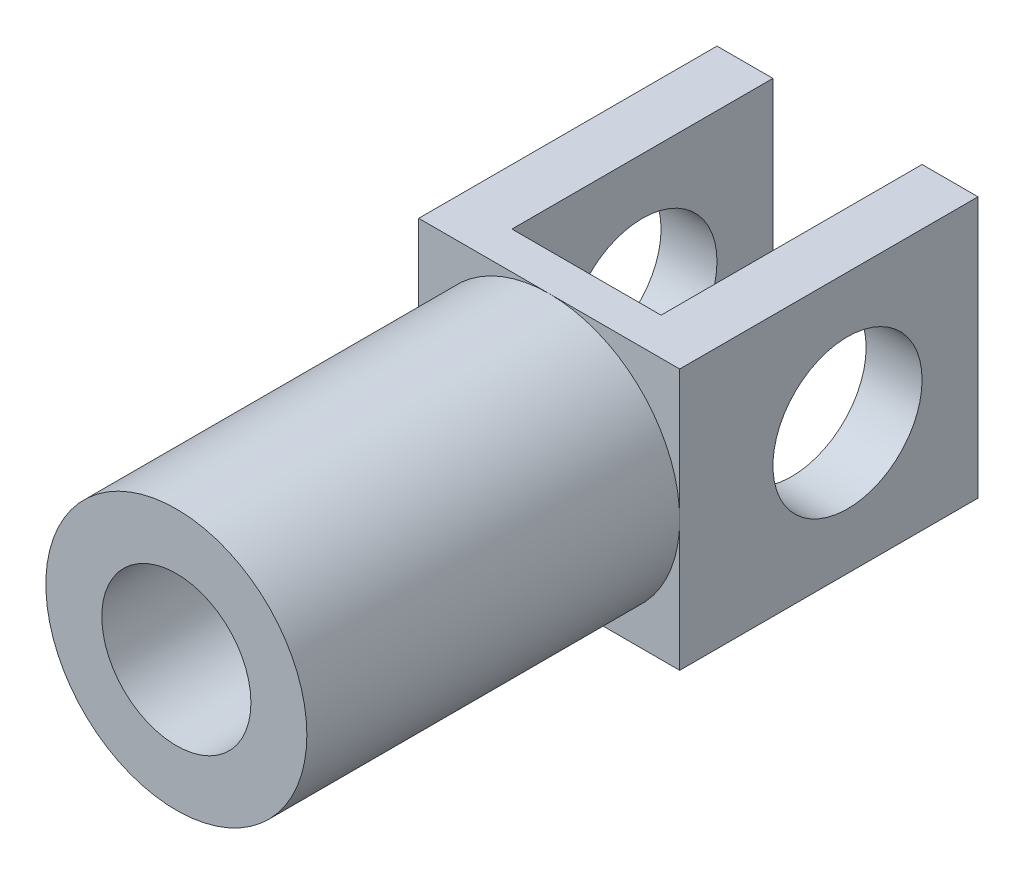
SolidWorks part; units mm, degrees
ref_plane "Front Plane" through (0, 0, 0) normal (0, 0, 1) x (1, 0, 0)
ref_plane "Top Plane" through (0, 0, 0) normal (0, 1, 0) x (1, 0, 0)
ref_plane "Right Plane" through (0, 0, 0) normal (1, 0, 0) x (0, 0, -1)
sketch "Sketch1" plane through (0, 0, 0) normal (0, 0, 1) x (1, 0, 0)
  circle A0 centre (0, 0) radius 2
  circle A1 centre (0, 0) radius 3.5
  dimension "D1" = 4
  dimension "D2" = 1.5
extrude "Boss-Extrude1" add sketch "Sketch1" along normal blind 10
sketch "Sketch2" plane through (0, 0, 0) normal (0, 0, 1) x (1, 0, 0)
  line L1 (-3.5, 3.5) -> (3.5, 3.5)
  line L2 (-3.5, 3.5) -> (-3.5, -3.5)
  line L3 (-3.5, -3.5) -> (3.5, -3.5)
  line L4 (3.5, 3.5) -> (3.5, -3.5)
  dimension "D1" = 7
  dimension "D2" = 3.5
  dimension "D3" = 3.5
  dimension "D4" = 7
extrude "Boss-Extrude2" add sketch "Sketch2" against normal blind 8
sketch "Sketch3" plane through (0, 0, 0) normal (0, 1, 0) x (1, 0, 0)
  line L1 (-2, 11) -> (2, 11)
  line L2 (-2, 11) -> (-2, 1)
  line L3 (-2, 1) -> (2, 1)
  line L4 (2, 11) -> (2, 1)
  line L5 (3.5, 0) -> (0, 0) construction
  line L6 (3.5, 8) -> (3.5, 0) construction
  dimension "D1" = 4
  dimension "D2" = 1
  dimension "D3" = 10
  dimension "D4" = 1.5
extrude "Cut-Extrude1" cut sketch "Sketch3" against normal through all both and the other way through all
sketch "Sketch4" plane through (0, 0, 0) normal (1, 0, 0) x (0, 0, -1)
  line L0 (8, -3.5) -> (8, 3.5) construction
  line L1 (8, 3.5) -> (0, 3.5) construction
  circle A0 centre (4.5, 0) radius 2
  dimension "D1" = 4
  dimension "D2" = 3.5
  dimension "D3" = 3.5
extrude "Cut-Extrude2" cut sketch "Sketch4" against normal through all both and the other way through all
